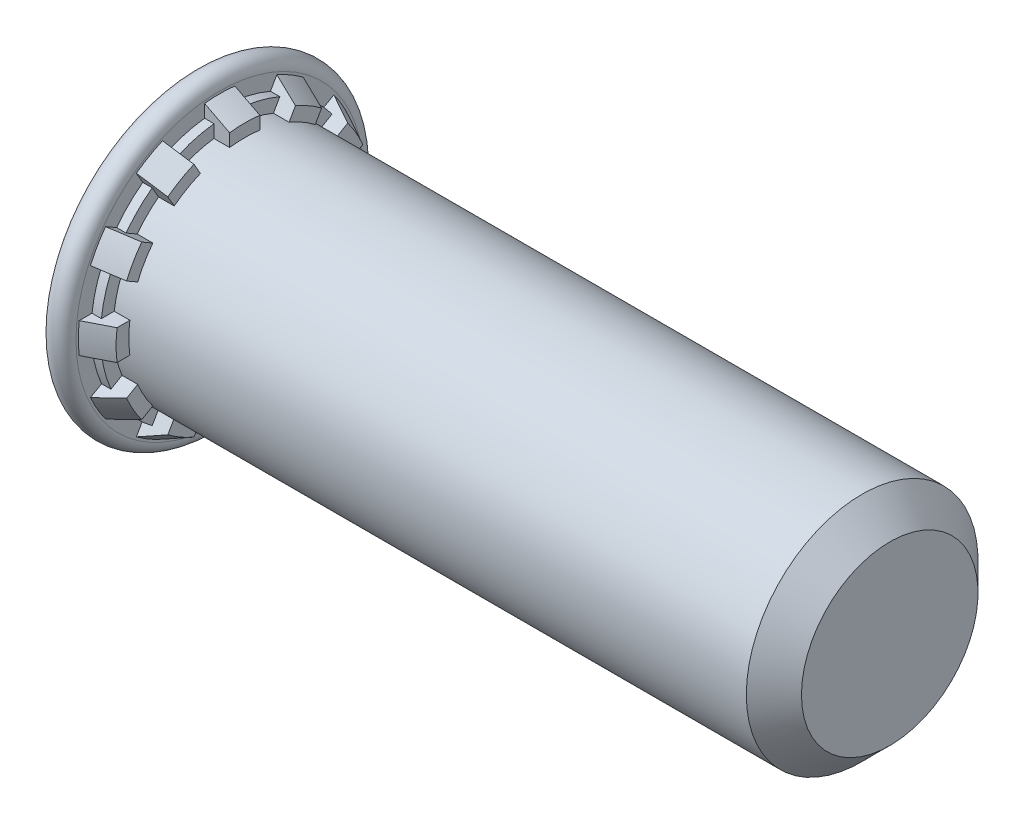
SolidWorks part; units mm, degrees
ref_plane "Plane1" through (0, 0, 0) normal (0, 0, 1) x (1, 0, 0)
ref_plane "Plane2" through (0, 0, 0) normal (0, 1, 0) x (1, 0, 0)
ref_plane "Plane3" through (0, 0, 0) normal (1, 0, 0) x (0, 0, -1)
sketch "BodySke" plane through (0, 0, 0) normal (0, 0, 1) x (1, 0, 0)
  line L0 (0, 0) -> (0, 3.9345)
  line L1 (0.6858, 3.9395) -> (0.6858, 3.8735)
  line L2 (0.6858, 3.8735) -> (1.3716, 3.5242)
  line L3 (1.3716, 3.175) -> (18.2943, 3.175)
  line L4 (19.05, 2.4193) -> (19.05, 0)
  line L5 (19.05, 0) -> (0, 0)
  line L6 (0, 0) -> (50.554, 0) construction
  line L7 (1.3716, 3.5242) -> (1.3716, 3.175)
  line L8 (19.05, 2.4193) -> (18.2943, 3.175)
  line L9 (-9.525, 4.2799) -> (9.525, 4.2799) construction
  line L11 (2.6416, 19.05) -> (2.6416, -3.175) construction
  line L13 (9.525, -4.2799) -> (-9.525, -4.2799) construction
  line L14 (0.0051, 3.9395) -> (0.0051, 3.9345)
  line L15 (0, 3.9345) -> (0.0051, 3.9345)
  arc A0 (0.0051, 3.9395) -> (0.6858, 3.9395) centre (0.3454, 3.9395) cw
  dimension "D2" = 0.0051
  dimension "D1" = 0.0051
  dimension "Diameter" = 6.35
  dimension "Length" = 19.05
  dimension "Body_ch_ang" = 45
  dimension "Minor_dia" = 4.8387
  dimension "Advance" = 1.27
  dimension "H_dia" = 8.5598
  dimension "Shoulder_lower_dia" = 7.747
  dimension "Shoulder_upper_dia" = 7.0485
  dimension "Shoulder_ht" = 1.3716
  dimension "T_dim" = 0.6858
revolve "BaseBody" add sketch "BodySke" angle 360 about L6
cosmetic thread "ThreadCosmetic" [suppressed] parameters "Thread_length"=15.621, "Thread_minor"=4.8387
sketch "ThdSchSke" plane through (0, 0, 0) normal (0, 0, 1) x (1, 0, 0)
  line L0 (3.429, -2.4193) -> (2.8999, -3.175)
  line L1 (3.429, -2.4193) -> (3.9581, -3.175)
  line L2 (3.9581, -3.175) -> (3.9581, -3.9688)
  line L3 (-3.175, 0) -> (5.1513, 0) construction
  line L5 (3.9581, -3.9688) -> (2.8999, -3.9688)
  line L6 (2.8999, -3.9688) -> (2.8999, -3.175)
  line L7 (0, 3.9345) -> (0, -3.9345) construction
  dimension "Thread_minor" = 4.8387
  dimension "Diameter" = 6.35
  dimension "Start" = 3.429
  dimension "SideAngle" = 55
  dimension "VeeAngle" = 70
  dimension "Overcut" = 7.9375
revolve "ThreadSchematic" [suppressed] cut sketch "ThdSchSke" angle 360 about L3
pattern_linear "ThdSchPat" [suppressed]
sketch "RibCut1Ske" plane through (1.3716, 0, 0) normal (1, 0, 0) x (0, 0, -1)
  line L0 (0.4144, 3.1478) -> (0.4144, 4.2598)
  line L1 (1.215, 2.9333) -> (1.771, 3.8963)
  line L2 (0, 0) -> (0, 4.9784) construction
  line L3 (0, 0) -> (0.4144, 3.1478) construction
  line L4 (0, 0) -> (1.215, 2.9333) construction
  arc A1 (1.215, 2.9333) -> (0.4144, 3.1478) centre (0, 0) ccw
  arc A2 (1.771, 3.8963) -> (0.4144, 4.2598) centre (0, 0) ccw
  dimension "Inner_dia" = 6.35
  dimension "Outer_dia" = 8.5598
  dimension "Rib_root_half_angle" = 7.5
  dimension "Rib_root_gap_angle" = 15
  dimension "Angle" = 30
extrude "RibCut1" cut sketch "RibCut1Ske" against normal blind 0.4286
sketch "RibCut2Ske" plane through (1.3716, 0, 0) normal (1, 0, 0) x (0, 0, -1)
  line L0 (0.4144, 3.4998) -> (0.4144, 4.2598)
  line L1 (1.391, 3.2381) -> (1.771, 3.8963)
  line L2 (0.4144, 3.1478) -> (0.4144, 4.9596) construction
  line L3 (0, 0) -> (0, 5.0239) construction
  line L4 (0, 0) -> (0.4144, 3.1478) construction
  line L5 (0, 0) -> (1.215, 2.9333) construction
  line L6 (1.215, 2.9333) -> (2.1244, 4.5085) construction
  arc A1 (1.391, 3.2381) -> (0.4144, 3.4998) centre (0, 0) ccw
  arc A2 (1.771, 3.8963) -> (0.4144, 4.2598) centre (0, 0) ccw
  circle A4 centre (0, 0) radius 3.175 construction
  dimension "Inner_dia" = 7.0485
  dimension "Outer_dia" = 8.5598
  dimension "Rib_root_dia" = 6.35
  dimension "Rib_root_half_angle" = 7.5
  dimension "Rib_root_gap_angle" = 15
  dimension "Angle" = 30
extrude "RibCut2" cut sketch "RibCut2Ske" against normal blind 0.6858
pattern_circular "RibCutsPat" count 12 every 30 about axis through (0, 0, 0) along (1, 0, 0) of "RibCut2", "RibCut1"
equation "' \"Length@BodySke\" = 0.75"
equation "' \"H_dia@BodySke\" = 0.337"
equation "' \"Start@ThdSchSke\" = 0.135"
equation "' \"Diameter@BodySke\" = 0.25"
equation "' \"Minor_dia@BodySke\" =0.1905"
equation "' \"Advance@BodySke\" = 0.05"
equation "\"T_dim@BodySke\" = \"Start@ThdSchSke\" * 0.2"
equation "\"Shoulder_ht@BodySke\" = \"Start@ThdSchSke\" * 0.4"
equation "\"Shoulder_lower_dia@BodySke\" = \"H_dia@BodySke\" - \"Start@ThdSchSke\" * 0.2 - .005"
equation "\"Shoulder_upper_dia@BodySke\" = ( \"Shoulder_lower_dia@BodySke\" + \"Diameter@BodySke\" ) /2"
equation "\"Num_ribs@RibCutsPat\" = 12"
equation "\"Angle@RibCutsPat\" = 360 / \"Num_ribs@RibCutsPat\""
equation "\"Angle@RibCut1Ske\" =\"Angle@RibCutsPat\""
equation "\"Rib_root_half_angle@RibCut1Ske\" = \"Angle@RibCut1Ske\" / 4"
equation "\"Rib_root_gap_angle@RibCut1Ske\" = \"Angle@RibCut1Ske\" - (2 * \"Rib_root_half_angle@RibCut1Ske\" )"
equation "\"Inner_dia@RibCut1Ske\" = \"Diameter@BodySke\""
equation "\"Outer_dia@RibCut1Ske\" = \"H_dia@BodySke\""
equation "\"Depth@RibCut1\" =  \"Start@ThdSchSke\" * 0.125"
equation "\"Angle@RibCut2Ske\" =\"Angle@RibCutsPat\""
equation "\"Rib_root_half_angle@RibCut2Ske\" = \"Angle@RibCut1Ske\" / 4"
equation "\"Rib_root_gap_angle@RibCut2Ske\" = \"Angle@RibCut1Ske\" - (2 * \"Rib_root_half_angle@RibCut1Ske\" )"
equation "\"Rib_root_dia@RibCut2Ske\" = \"Diameter@BodySke\""
equation "\"Inner_dia@RibCut2Ske\" = \"Shoulder_upper_dia@BodySke\""
equation "\"Outer_dia@RibCut2Ske\" = \"H_dia@BodySke\""
equation "\"Depth@RibCut2\" =  \"Start@ThdSchSke\" * 0.2"
equation "\"Thread_length@ThreadCosmetic\" = \"Length@BodySke\" - \"Start@ThdSchSke\""
equation "\"Thread_minor@ThreadCosmetic\" = \"Minor_dia@BodySke\""
equation "\"Thread_minor@ThdSchSke\" = \"Minor_dia@BodySke\""
equation "\"Diameter@ThdSchSke\" = \"Diameter@BodySke\""
equation "\"Overcut@ThdSchSke\" = \"Diameter@BodySke\" * 1.25"
equation "\"Num_threads@ThdSchPat\" = int( \"Thread_length@ThreadCosmetic\" / \"Advance@BodySke\" + 0.999 )  + 1"
equation "\"Advance@ThdSchPat\" = \"Thread_length@ThreadCosmetic\" /  (\"Num_threads@ThdSchPat\" - 1) 'relax it"
equation "\"Num_threads@ThdSchPat\" = \"Num_threads@ThdSchPat\" - sgn( \"Num_threads@ThdSchPat\" - 1) '---chamfered tips only---"
